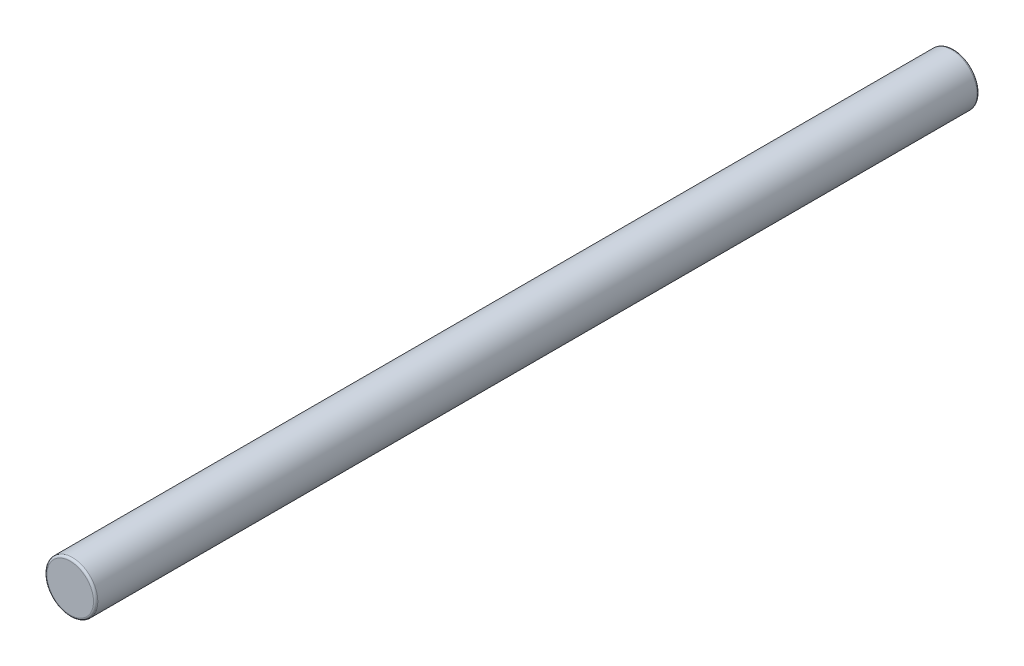
SolidWorks part; units mm, degrees
ref_plane "Front Plane" through (0, 0, 0) normal (0, 0, 1) x (1, 0, 0)
ref_plane "Top Plane" through (0, 0, 0) normal (0, 1, 0) x (1, 0, 0)
ref_plane "Right Plane" through (0, 0, 0) normal (1, 0, 0) x (0, 0, -1)
sketch "Sketch1" plane through (0, 0, 0) normal (0, 0, 1) x (1, 0, 0)
  circle A0 centre (0, 0) radius 1.5
  dimension "D1" = 3
extrude "Boss-Extrude1" add sketch "Sketch1" along normal mid plane 52
fillet "Fillet1" radius 0.127 2 edges at (1.5, 0, -26) (1.5, 0, 26)
